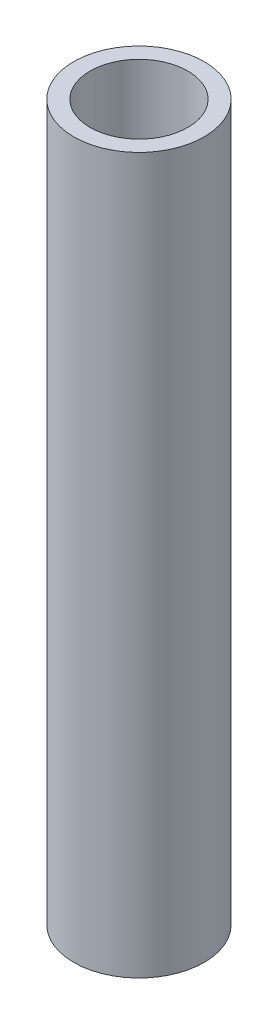
SolidWorks part; units mm, degrees
ref_plane "Front Plane" through (0, 0, 0) normal (0, 0, 1) x (1, 0, 0)
ref_plane "Top Plane" through (0, 0, 0) normal (0, 1, 0) x (1, 0, 0)
ref_plane "Right Plane" through (0, 0, 0) normal (1, 0, 0) x (0, 0, -1)
sketch "Sketch1" plane through (0, 0, 0) normal (0, 1, 0) x (1, 0, 0)
  circle A0 centre (0, 0) radius 6
  circle A1 centre (0, 0) radius 4.5
  dimension "D1" = 12
  dimension "D2" = 9
extrude "Boss-Extrude1" add sketch "Sketch1" along normal blind 65.8
